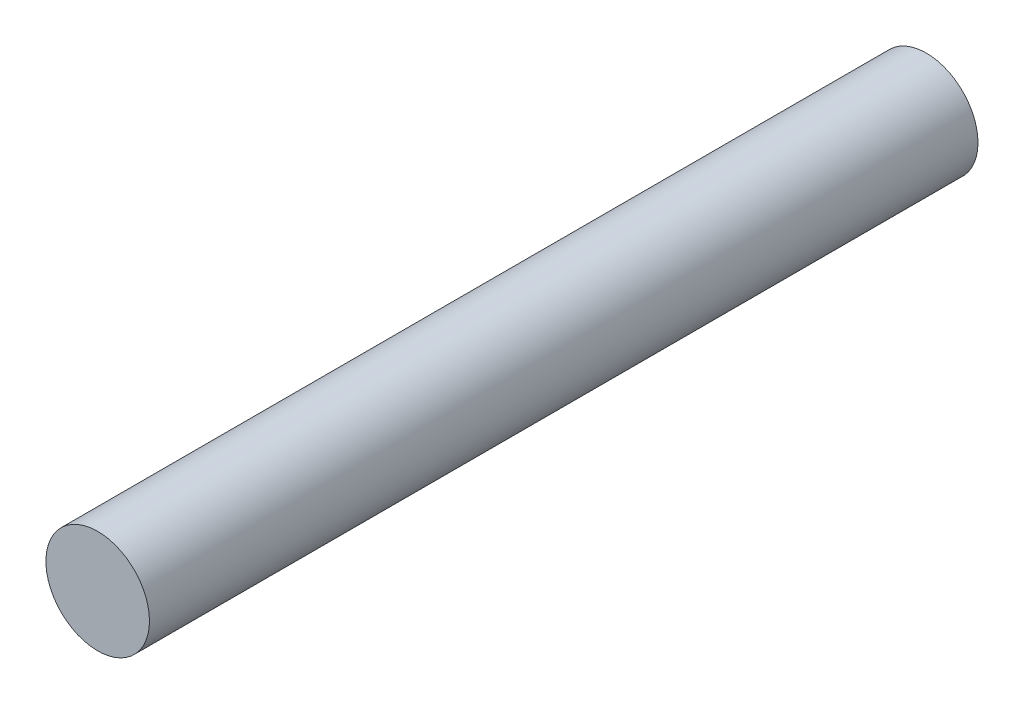
SolidWorks part; units mm, degrees
ref_plane "Front Plane" through (0, 0, 0) normal (0, 0, 1) x (1, 0, 0)
ref_plane "Top Plane" through (0, 0, 0) normal (0, 1, 0) x (1, 0, 0)
ref_plane "Right Plane" through (0, 0, 0) normal (1, 0, 0) x (0, 0, -1)
sketch "Sketch1" plane through (0, 0, 0) normal (0, 0, 1) x (1, 0, 0)
  circle A0 centre (0, 0) radius 4.7625
  dimension "D1" = 9.525
extrude "Boss-Extrude1" add sketch "Sketch1" against normal blind 76.2
